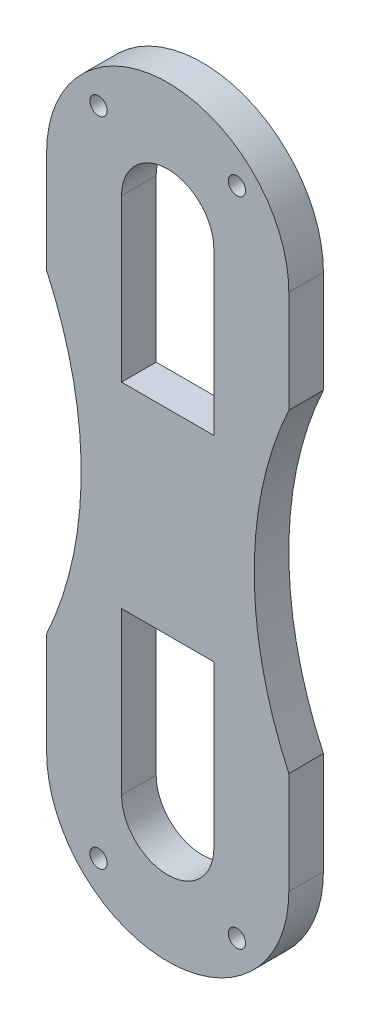
SolidWorks part; units mm, degrees
ref_plane "前视基准面" through (0, 0, 0) normal (0, 0, 1) x (1, 0, 0)
ref_plane "上视基准面" through (0, 0, 0) normal (0, 1, 0) x (1, 0, 0)
ref_plane "右视基准面" through (0, 0, 0) normal (1, 0, 0) x (0, 0, -1)
sketch "草图1" plane through (0, 0, 0) normal (0, 0, 1) x (1, 0, 0)
  line L0 (0, 0) -> (0, 22.5) construction
  line L1 (10.5, -13.6382) -> (10.5, -22.5)
  line L2 (-10.5, 22.5) -> (-10.5, 13.6382)
  line L3 (-4, -22.5) -> (-4, -8.5)
  line L4 (10.5, 22.5) -> (10.5, 13.6382)
  line L5 (-10.5, -13.6382) -> (-10.5, -22.5)
  line L6 (4, -22.5) -> (4, -8.5)
  line L7 (0, 0) -> (40, 0) construction
  line L8 (-4, 22.5) -> (-4, 8.5)
  line L9 (-4, 8.5) -> (4, 8.5)
  line L10 (4, 22.5) -> (4, 8.5)
  line L11 (-4, -8.5) -> (4, -8.5)
  arc A0 (10.5, 22.5) -> (-10.5, 22.5) centre (0, 22.5) ccw
  arc A1 (10.5, -22.5) -> (-10.5, -22.5) centre (0, -22.5) cw
  arc A2 (10.5, 13.6382) -> (10.5, -13.6382) centre (40, 0) ccw
  arc A3 (-10.5, 13.6382) -> (-10.5, -13.6382) centre (-40, 0) cw
  arc A4 (4, 22.5) -> (-4, 22.5) centre (0, 22.5) ccw
  arc A5 (4, -22.5) -> (-4, -22.5) centre (0, -22.5) cw
  circle A6 centre (0, 10) radius 0.75
  circle A7 centre (0, -10) radius 0.75
  circle A8 centre (-6, 28.25) radius 0.75
  circle A9 centre (6, 28.25) radius 0.75
  circle A10 centre (6, -28.25) radius 0.75
  circle A11 centre (-6, -28.25) radius 0.75
  point P0 (0, 0)
  point P15 (0, 26.5)
  point P16 (0, 19.246)
  point P21 (-4, 15.5)
  point P22 (4, 15.5)
  dimension "D3" = 21
  dimension "D2" = 65
  dimension "D6" = 8
  dimension "D9" = 1.5
  dimension "D11" = 1.5
  dimension "D1" = 21
  dimension "D4" = 45
  dimension "D5" = 40
  dimension "D7" = 8
  dimension "D8" = 18
  dimension "D10" = 20
  dimension "D12" = 12
  dimension "D13" = 56.5
extrude "凸台-拉伸1" add sketch "草图1" along normal blind 3 contours L2 A3 L5 A1 L1 A2 L4 A0 A9 A8 A4 L10 L9 L8 L6 A5 L3 L11 A10 A11
sketch "草图2" plane through (0, 0, 0) normal (0, 0, -1) x (-1, 0, 0)
  line L0 (4, 24.5) -> (4, 20.5)
  line L1 (0, 22.5) -> (0, 24.5) construction
  line L2 (4, 22.5) -> (4, 8.5) construction
  line L3 (4, 20.5) -> (-4, 20.5)
  line L4 (-4, 22.5) -> (-4, 8.5) construction
  line L5 (-4, 20.5) -> (-4, 24.5)
  line L6 (0, 0) -> (19.7984, 0) construction
  line L7 (4, -24.5) -> (4, -20.5)
  line L8 (-4, -20.5) -> (-4, -24.5)
  line L9 (4, -20.5) -> (-4, -20.5)
  arc A0 (4, 24.5) -> (-4, 24.5) centre (0, 24.5) ccw
  arc A1 (4, 22.5) -> (-4, 22.5) centre (0, 22.5) ccw construction
  arc A2 (4, -24.5) -> (-4, -24.5) centre (0, -24.5) cw
  dimension "D1" = 2
